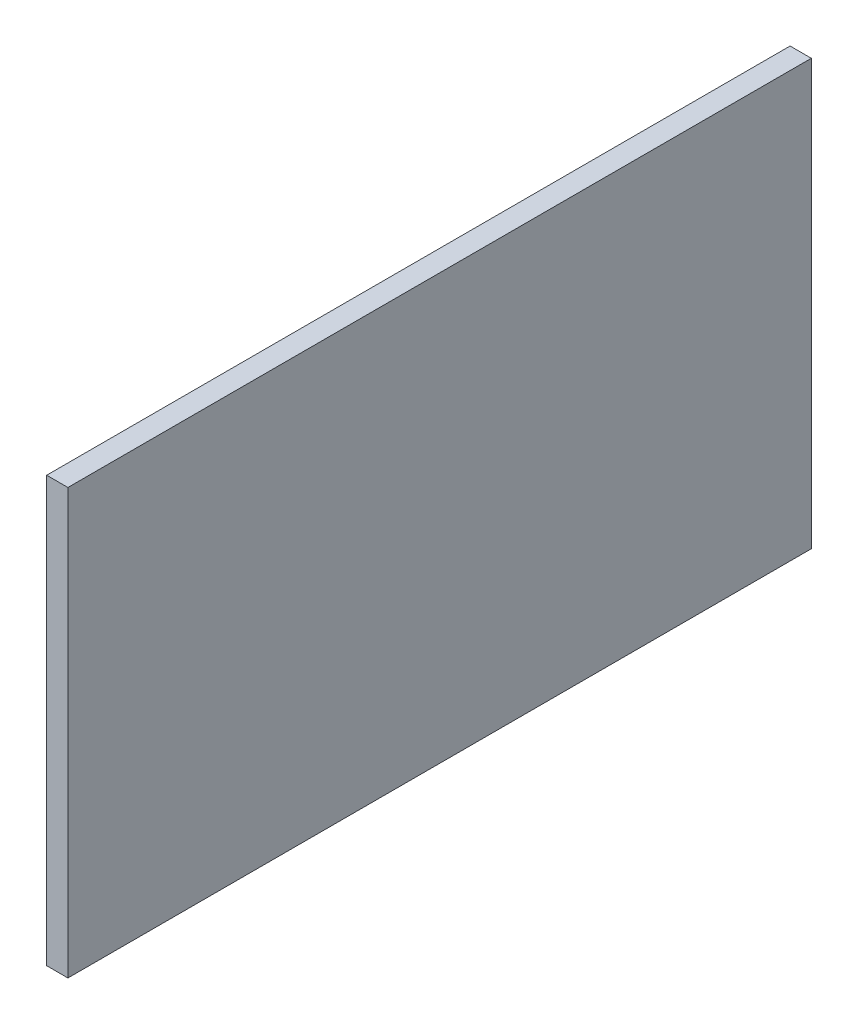
SolidWorks part; units mm, degrees
ref_plane "Přední rovina" through (0, 0, 0) normal (0, 0, 1) x (1, 0, 0)
ref_plane "Horní rovina" through (0, 0, 0) normal (0, 1, 0) x (1, 0, 0)
ref_plane "Pravá rovina" through (0, 0, 0) normal (1, 0, 0) x (0, 0, -1)
sketch "Skica1" plane through (0, 0, 0) normal (1, 0, 0) x (0, 0, -1)
  line L1 (-175, 100) -> (175, 100)
  line L2 (-175, 100) -> (-175, -100)
  line L3 (-175, -100) -> (175, -100)
  line L4 (175, 100) -> (175, -100)
  line L5 (-175, 100) -> (175, -100) construction
  line L6 (-175, -100) -> (175, 100) construction
  point P0 (0, 0)
  dimension "D1" = 200
  dimension "D2" = 350
extrude "Vysunout1" add sketch "Skica1" along normal blind 10
sketch "Skica2" plane through (0, 0, 0) normal (-1, 0, 0) x (0, 0, 1)
  line L0 (-175, -100) -> (-175, 100) construction
  line L1 (-175, 100) -> (175, 100) construction
  circle A0 centre (-140, 75) radius 15
  dimension "D2" = 25
  dimension "D3" = 30
  dimension "D1" = 35
extrude "Vysunout2" add sketch "Skica2" along normal blind 5
fillet "Zaoblit1" radius 1.5 1 edges at (-5, 75, -125)
pattern_linear "LinPole1" count 2 spacing 280 along (0, 0, 1) count 2 spacing 150 along (0, -1, 0) of "Zaoblit1", "Vysunout2"
